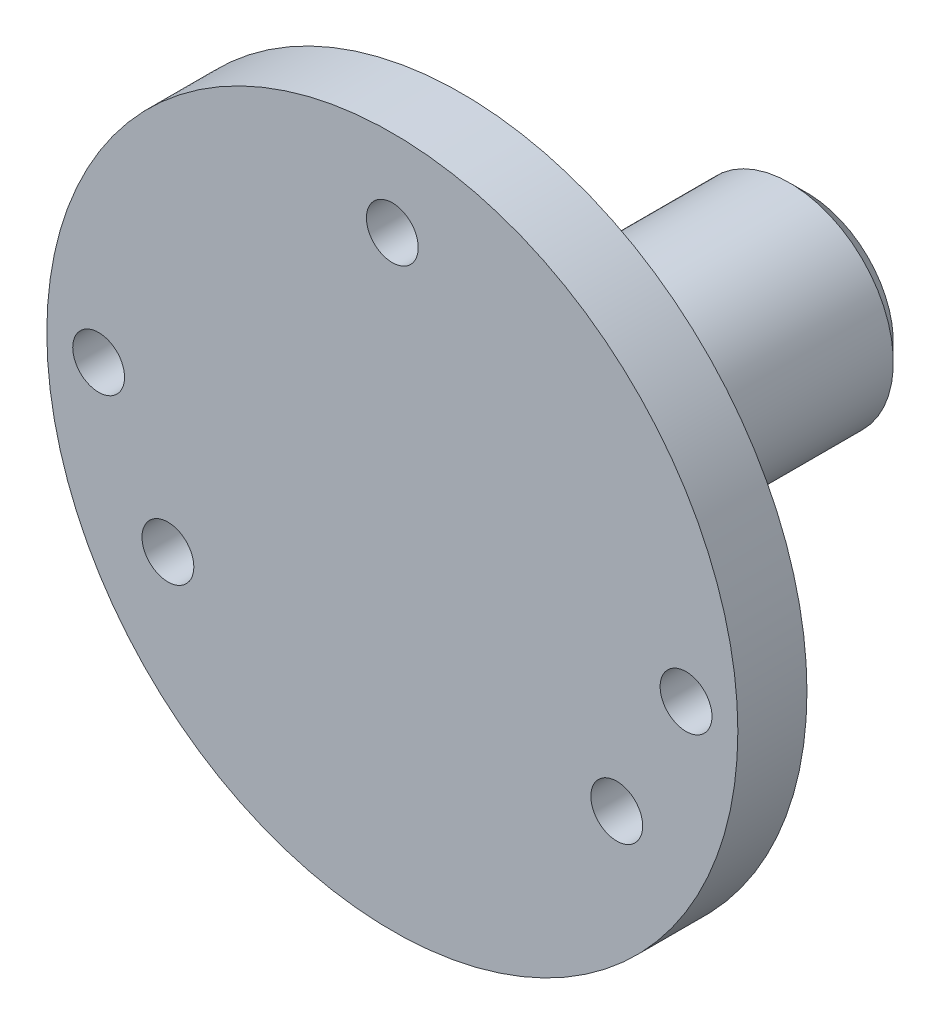
SolidWorks part; units mm, degrees
ref_plane "Front Plane" through (0, 0, 0) normal (0, 0, 1) x (1, 0, 0)
ref_plane "Top Plane" through (0, 0, 0) normal (0, 1, 0) x (1, 0, 0)
ref_plane "Right Plane" through (0, 0, 0) normal (1, 0, 0) x (0, 0, -1)
sketch "Sketch1" plane through (0, 0, 0) normal (0, 0, 1) x (1, 0, 0)
  circle A0 centre (0, 0) radius 5.5
  circle A1 centre (0, 0) radius 10
  dimension "D1" = 11
  dimension "D2" = 20
extrude "Boss-Extrude1" add sketch "Sketch1" along normal blind 2
sketch "Sketch3" plane through (0, 0, 0) normal (0, 0, -1) x (-1, 0, 0)
  circle A0 centre (0, 0) radius 3
  dimension "D1" = 6
extrude "Boss-Extrude2" add sketch "Sketch3" along normal blind 12 separate body
sketch "Sketch4" plane through (0, 0, 0) normal (0, 0, -1) x (-1, 0, 0)
  circle A0 centre (0, 0) radius 10 construction
  circle A2 centre (0, 0) radius 10
  circle A4 centre (0, 0) radius 3 construction
  circle A5 centre (0, 0) radius 3
extrude "Boss-Extrude3" add sketch "Sketch4" along normal blind 2
chamfer "Chamfer2" distance 1 angle 45 1 edges at (-3, 0, -2)
chamfer "Chamfer4" distance 0.5 angle 45 1 edges at (-3, 0, -12)
sketch "Sketch5" plane through (0, 0, -2) normal (0, 0, -1) x (-1, 0, 0)
  line L0 (-10, 0) -> (10, 0) construction
  circle A0 centre (0, 0) radius 10 construction
  circle A1 centre (-8.5, 0) radius 0.75
  circle A2 centre (8.5, 0) radius 0.75
  circle A3 centre (0, 0) radius 4 construction
  point P9 (4, 0)
  dimension "D1" = 1.5
  dimension "D2" = 1.5
  dimension "D3" = 1.5
  dimension "D4" = 1.5
extrude "Cut-Extrude1" cut sketch "Sketch5" against normal up to next
sketch "Sketch6" plane through (0, 0, 2) normal (0, 0, 1) x (1, 0, 0)
  circle A0 centre (0, 0) radius 6.25
  circle A1 centre (0, 0) radius 5.5 construction
  circle A2 centre (0, 0) radius 5.5
  point P2 (0, 0)
  point P3 (1.3531, -0.9423)
  point P4 (0, 0)
  dimension "D1" = 0.75
extrude "Boss-Extrude4" add sketch "Sketch6" along normal blind 26
sketch "Sketch7" plane through (0, 0, -2) normal (0, 0, -1) x (-1, 0, 0)
  circle A0 centre (0, 0) radius 7.5 construction
  circle A1 centre (0, 7.5) radius 0.75
  circle A2 centre (6.4952, -3.75) radius 0.75
  circle A3 centre (-6.4952, -3.75) radius 0.75
  point P5 (0.3441, 6.9915)
  point P6 (0, 0)
  point P7 (0, 0)
  point P14 (0, 0)
  dimension "D1" = 15
  dimension "D2" = 1.5
  dimension "D3" = 3
extrude "Cut-Extrude2" cut sketch "Sketch7" against normal up to next
sketch "Sketch9" plane through (0, 0, 28) normal (0, 0, 1) x (1, 0, 0)
  circle A0 centre (0, 0) radius 17.3588
extrude "Cut-Extrude3" cut sketch "Sketch9" against normal blind 28
